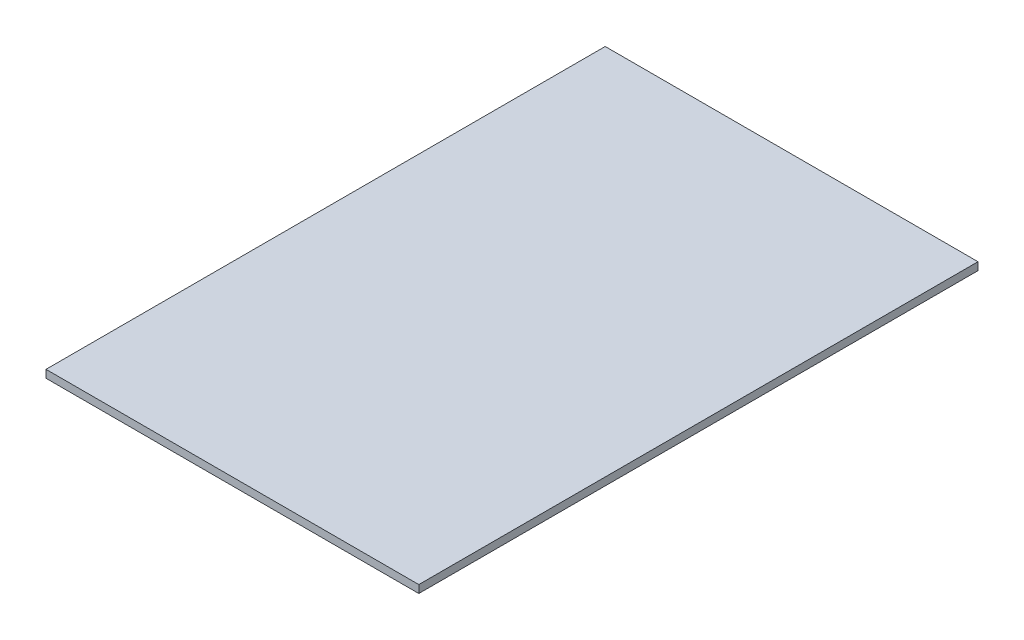
SolidWorks part; units mm, degrees
material "Oak"
ref_plane "Front Plane" through (0, 0, 0) normal (0, 0, 1) x (1, 0, 0)
ref_plane "Top Plane" through (0, 0, 0) normal (0, 1, 0) x (1, 0, 0)
ref_plane "Right Plane" through (0, 0, 0) normal (1, 0, 0) x (0, 0, -1)
sketch "Sketch1" plane through (0, 0, 0) normal (0, 1, 0) x (1, 0, 0)
  line L1 (-304.8, -457.2) -> (304.8, -457.2)
  line L2 (-304.8, -457.2) -> (-304.8, 457.2)
  line L3 (-304.8, 457.2) -> (304.8, 457.2)
  line L4 (304.8, -457.2) -> (304.8, 457.2)
  line L5 (-304.8, -457.2) -> (304.8, 457.2) construction
  line L6 (-304.8, 457.2) -> (304.8, -457.2) construction
  point P0 (0, 0)
  dimension "D1" = 609.6
  dimension "D2" = 914.4
extrude "Boss-Extrude1" add sketch "Sketch1" along normal mid plane 12.7
